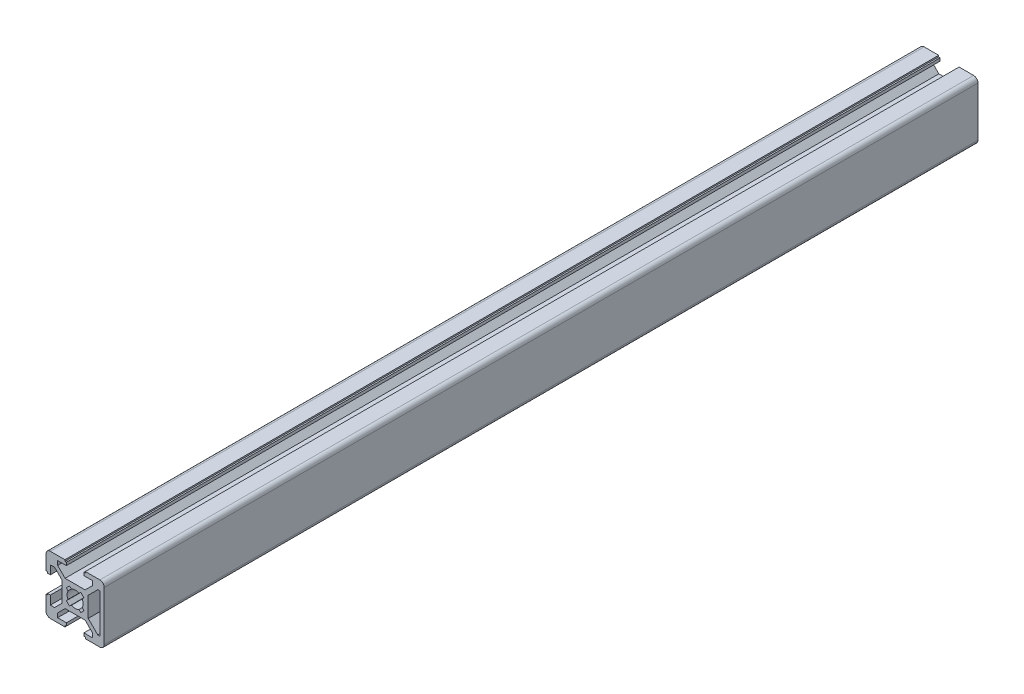
SolidWorks part; units mm, degrees
ref_plane "Front Plane" through (0, 0, 0) normal (0, 0, 1) x (1, 0, 0)
ref_plane "Top Plane" through (0, 0, 0) normal (0, 1, 0) x (1, 0, 0)
ref_plane "Right Plane" through (0, 0, 0) normal (1, 0, 0) x (0, 0, -1)
sketch "Sketch1" plane through (0, 0, 0) normal (0, 0, 1) x (1, 0, 0)
  line L12 (8.5, 6.7322) -> (7.7929, 6.7322)
  line L13 (8.5, -6.7322) -> (8.5, 6.7322)
  line L14 (7.7929, -6.7322) -> (8.5, -6.7322)
  line L15 (4.5, -3.4393) -> (7.7929, -6.7322)
  line L16 (4.5, 3.4393) -> (4.5, -3.4393)
  line L17 (7.7929, 6.7322) -> (4.5, 3.4393)
  line L36 (-3.0002, 1.9496) -> (-2.4356, 1.2768)
  line L37 (-1.9496, 3.0002) -> (-3.0002, 1.9496)
  line L38 (-1.2768, 2.4356) -> (-1.9496, 3.0002)
  line L39 (1.9496, 3.0002) -> (1.2768, 2.4356)
  line L40 (3.0002, 1.9496) -> (1.9496, 3.0002)
  line L41 (2.4356, 1.2768) -> (3.0002, 1.9496)
  line L42 (3.0002, -1.9496) -> (2.4356, -1.2768)
  line L43 (1.9496, -3.0002) -> (3.0002, -1.9496)
  line L44 (1.2768, -2.4356) -> (1.9496, -3.0002)
  line L45 (-1.9496, -3.0002) -> (-1.2768, -2.4356)
  line L46 (-3.0002, -1.9496) -> (-1.9496, -3.0002)
  line L47 (-2.4356, -1.2768) -> (-3.0002, -1.9496)
  line L128 (-3.4393, -4.5) -> (3.4393, -4.5)
  line L129 (3.4393, -4.5) -> (6, -7.0607)
  line L130 (6, -7.0607) -> (6, -8.5)
  line L131 (6, -8.5) -> (3, -8.5)
  line L132 (3, -8.5) -> (3, -9.5)
  line L133 (3, -9.5) -> (3.5, -9.5)
  line L134 (3.5, -9.5) -> (3.5, -10)
  line L135 (3.5, -10) -> (8.5, -10)
  line L136 (10, -8.5) -> (10, 8.5)
  line L137 (8.5, 10) -> (3.5, 10)
  line L138 (3.5, 10) -> (3.5, 9.5)
  line L139 (3.5, 9.5) -> (3, 9.5)
  line L140 (3, 9.5) -> (3, 8.5)
  line L141 (3, 8.5) -> (6, 8.5)
  line L142 (6, 8.5) -> (6, 7.0607)
  line L143 (6, 7.0607) -> (3.4393, 4.5)
  line L144 (3.4393, 4.5) -> (-3.4393, 4.5)
  line L145 (-3.4393, 4.5) -> (-6, 7.0607)
  line L146 (-6, 7.0607) -> (-6, 8.5)
  line L147 (-6, 8.5) -> (-3, 8.5)
  line L148 (-3, 8.5) -> (-3, 9.5)
  line L149 (-3, 9.5) -> (-3.5, 9.5)
  line L150 (-3.5, 9.5) -> (-3.5, 10)
  line L151 (-3.5, 10) -> (-8.5, 10)
  line L152 (-10, 8.5) -> (-10, 3.5)
  line L153 (-10, 3.5) -> (-9.5, 3.5)
  line L154 (-9.5, 3.5) -> (-9.5, 3)
  line L155 (-9.5, 3) -> (-8.5, 3)
  line L156 (-8.5, 3) -> (-8.5, 6)
  line L157 (-8.5, 6) -> (-7.0607, 6)
  line L158 (-7.0607, 6) -> (-4.5, 3.4393)
  line L159 (-4.5, 3.4393) -> (-4.5, -3.4393)
  line L160 (-4.5, -3.4393) -> (-7.0607, -6)
  line L161 (-7.0607, -6) -> (-8.5, -6)
  line L162 (-8.5, -6) -> (-8.5, -3)
  line L163 (-8.5, -3) -> (-9.5, -3)
  line L164 (-9.5, -3) -> (-9.5, -3.5)
  line L165 (-9.5, -3.5) -> (-10, -3.5)
  line L166 (-10, -3.5) -> (-10, -8.5)
  line L167 (-8.5, -10) -> (-3.5, -10)
  line L168 (-3.5, -10) -> (-3.5, -9.5)
  line L169 (-3.5, -9.5) -> (-3, -9.5)
  line L170 (-3, -9.5) -> (-3, -8.5)
  line L171 (-3, -8.5) -> (-6, -8.5)
  line L172 (-6, -8.5) -> (-6, -7.0607)
  line L173 (-6, -7.0607) -> (-3.4393, -4.5)
  arc A8 (-2.4356, 1.2768) -> (-2.4356, -1.2768) centre (0, 0) ccw
  arc A9 (1.2768, 2.4356) -> (-1.2768, 2.4356) centre (0, 0) ccw
  arc A10 (2.4356, -1.2768) -> (2.4356, 1.2768) centre (0, 0) ccw
  arc A11 (-1.2768, -2.4356) -> (1.2768, -2.4356) centre (0, 0) ccw
  arc A16 (8.5, -10) -> (10, -8.5) centre (8.5, -8.5) ccw
  arc A17 (10, 8.5) -> (8.5, 10) centre (8.5, 8.5) ccw
  arc A18 (-8.5, 10) -> (-10, 8.5) centre (-8.5, 8.5) ccw
  arc A19 (-10, -8.5) -> (-8.5, -10) centre (-8.5, -8.5) ccw
extrude "Boss-Extrude1" add sketch "Sketch1" along normal blind 3000
sketch "Sketch2" plane through (0, 0, 3000) normal (0, 0, 1) x (1, 0, 0)
  line L46 (-6, -7.0607) -> (-3.4393, -4.5)
  line L47 (-3.4393, -4.5) -> (3.4393, -4.5)
  line L48 (3.4393, -4.5) -> (6, -7.0607)
  line L49 (6, -7.0607) -> (6, -8.5)
  line L50 (6, -8.5) -> (3, -8.5)
  line L51 (3, -8.5) -> (3, -9.5)
  line L52 (3, -9.5) -> (3.5, -9.5)
  line L53 (3.5, -9.5) -> (3.5, -10)
  line L54 (3.5, -10) -> (8.5, -10)
  line L55 (10, -8.5) -> (10, 8.5)
  line L56 (8.5, 10) -> (3.5, 10)
  line L57 (3.5, 10) -> (3.5, 9.5)
  line L58 (3.5, 9.5) -> (3, 9.5)
  line L59 (3, 9.5) -> (3, 8.5)
  line L60 (3, 8.5) -> (6, 8.5)
  line L61 (6, 8.5) -> (6, 7.0607)
  line L62 (6, 7.0607) -> (3.4393, 4.5)
  line L63 (3.4393, 4.5) -> (-3.4393, 4.5)
  line L64 (-3.4393, 4.5) -> (-6, 7.0607)
  line L65 (-6, 7.0607) -> (-6, 8.5)
  line L66 (-6, 8.5) -> (-3, 8.5)
  line L67 (-3, 8.5) -> (-3, 9.5)
  line L68 (-3, 9.5) -> (-3.5, 9.5)
  line L69 (-3.5, 9.5) -> (-3.5, 10)
  line L70 (-3.5, 10) -> (-8.5, 10)
  line L71 (-10, 8.5) -> (-10, 3.5)
  line L72 (-10, 3.5) -> (-9.5, 3.5)
  line L73 (-9.5, 3.5) -> (-9.5, 3)
  line L74 (-9.5, 3) -> (-8.5, 3)
  line L75 (-8.5, 3) -> (-8.5, 6)
  line L76 (-8.5, 6) -> (-7.0607, 6)
  line L77 (-7.0607, 6) -> (-4.5, 3.4393)
  line L78 (-4.5, 3.4393) -> (-4.5, -3.4393)
  line L79 (-4.5, -3.4393) -> (-7.0607, -6)
  line L80 (-7.0607, -6) -> (-8.5, -6)
  line L81 (-8.5, -6) -> (-8.5, -3)
  line L82 (-8.5, -3) -> (-9.5, -3)
  line L83 (-9.5, -3) -> (-9.5, -3.5)
  line L84 (-9.5, -3.5) -> (-10, -3.5)
  line L85 (-10, -3.5) -> (-10, -8.5)
  line L86 (-8.5, -10) -> (-3.5, -10)
  line L87 (-3.5, -10) -> (-3.5, -9.5)
  line L88 (-3.5, -9.5) -> (-3, -9.5)
  line L89 (-3, -9.5) -> (-3, -8.5)
  line L90 (-3, -8.5) -> (-6, -8.5)
  line L91 (-6, -8.5) -> (-6, -7.0607)
  line L92 (-6, -7.0607) -> (-3.4393, -4.5)
  line L93 (-3.4393, -4.5) -> (3.4393, -4.5)
  line L94 (3.4393, -4.5) -> (6, -7.0607)
  line L95 (6, -7.0607) -> (6, -8.5)
  line L96 (6, -8.5) -> (3, -8.5)
  line L97 (3, -8.5) -> (3, -9.5)
  line L98 (3, -9.5) -> (3.5, -9.5)
  line L99 (3.5, -9.5) -> (3.5, -10)
  line L100 (3.5, -10) -> (8.5, -10)
  line L101 (10, -8.5) -> (10, 8.5)
  line L102 (8.5, 10) -> (3.5, 10)
  line L103 (3.5, 10) -> (3.5, 9.5)
  line L104 (3.5, 9.5) -> (3, 9.5)
  line L105 (3, 9.5) -> (3, 8.5)
  line L106 (3, 8.5) -> (6, 8.5)
  line L107 (6, 8.5) -> (6, 7.0607)
  line L108 (6, 7.0607) -> (3.4393, 4.5)
  line L109 (3.4393, 4.5) -> (-3.4393, 4.5)
  line L110 (-3.4393, 4.5) -> (-6, 7.0607)
  line L111 (-6, 7.0607) -> (-6, 8.5)
  line L112 (-6, 8.5) -> (-3, 8.5)
  line L113 (-3, 8.5) -> (-3, 9.5)
  line L114 (-3, 9.5) -> (-3.5, 9.5)
  line L115 (-3.5, 9.5) -> (-3.5, 10)
  line L116 (-3.5, 10) -> (-8.5, 10)
  line L117 (-10, 8.5) -> (-10, 3.5)
  line L118 (-10, 3.5) -> (-9.5, 3.5)
  line L119 (-9.5, 3.5) -> (-9.5, 3)
  line L120 (-9.5, 3) -> (-8.5, 3)
  line L121 (-8.5, 3) -> (-8.5, 6)
  line L122 (-8.5, 6) -> (-7.0607, 6)
  line L123 (-7.0607, 6) -> (-4.5, 3.4393)
  line L124 (-4.5, 3.4393) -> (-4.5, -3.4393)
  line L125 (-4.5, -3.4393) -> (-7.0607, -6)
  line L126 (-7.0607, -6) -> (-8.5, -6)
  line L127 (-8.5, -6) -> (-8.5, -3)
  line L128 (-8.5, -3) -> (-9.5, -3)
  line L129 (-9.5, -3) -> (-9.5, -3.5)
  line L130 (-9.5, -3.5) -> (-10, -3.5)
  line L131 (-10, -3.5) -> (-10, -8.5)
  line L132 (-8.5, -10) -> (-3.5, -10)
  line L133 (-3.5, -10) -> (-3.5, -9.5)
  line L134 (-3.5, -9.5) -> (-3, -9.5)
  line L135 (-3, -9.5) -> (-3, -8.5)
  line L136 (-3, -8.5) -> (-6, -8.5)
  line L137 (-6, -8.5) -> (-6, -7.0607)
  arc A4 (8.5, -10) -> (10, -8.5) centre (8.5, -8.5) ccw
  arc A5 (10, 8.5) -> (8.5, 10) centre (8.5, 8.5) ccw
  arc A6 (-8.5, 10) -> (-10, 8.5) centre (-8.5, 8.5) ccw
  arc A7 (-10, -8.5) -> (-8.5, -10) centre (-8.5, -8.5) ccw
  arc A8 (8.5, -10) -> (10, -8.5) centre (8.5, -8.5) ccw
  arc A9 (10, 8.5) -> (8.5, 10) centre (8.5, 8.5) ccw
  arc A10 (-8.5, 10) -> (-10, 8.5) centre (-8.5, 8.5) ccw
  arc A11 (-10, -8.5) -> (-8.5, -10) centre (-8.5, -8.5) ccw
  dimension "D1" = 0
extrude "Cut-Extrude1" cut sketch "Sketch2" against normal offset from surface (2700 mm away) 300 up to face at (6.931, 0, 0)
sketch "Sketch3" [suppressed] plane through (0, 0, 3000) normal (0, 0, 1) x (1, 0, 0)
  line L46 (-6, -7.0607) -> (-3.4393, -4.5)
  line L47 (-3.4393, -4.5) -> (3.4393, -4.5)
  line L48 (3.4393, -4.5) -> (6, -7.0607)
  line L49 (6, -7.0607) -> (6, -8.5)
  line L50 (6, -8.5) -> (3, -8.5)
  line L51 (3, -8.5) -> (3, -9.5)
  line L52 (3, -9.5) -> (3.5, -9.5)
  line L53 (3.5, -9.5) -> (3.5, -10)
  line L54 (3.5, -10) -> (8.5, -10)
  line L55 (10, -8.5) -> (10, 8.5)
  line L56 (8.5, 10) -> (3.5, 10)
  line L57 (3.5, 10) -> (3.5, 9.5)
  line L58 (3.5, 9.5) -> (3, 9.5)
  line L59 (3, 9.5) -> (3, 8.5)
  line L60 (3, 8.5) -> (6, 8.5)
  line L61 (6, 8.5) -> (6, 7.0607)
  line L62 (6, 7.0607) -> (3.4393, 4.5)
  line L63 (3.4393, 4.5) -> (-3.4393, 4.5)
  line L64 (-3.4393, 4.5) -> (-6, 7.0607)
  line L65 (-6, 7.0607) -> (-6, 8.5)
  line L66 (-6, 8.5) -> (-3, 8.5)
  line L67 (-3, 8.5) -> (-3, 9.5)
  line L68 (-3, 9.5) -> (-3.5, 9.5)
  line L69 (-3.5, 9.5) -> (-3.5, 10)
  line L70 (-3.5, 10) -> (-8.5, 10)
  line L71 (-10, 8.5) -> (-10, 3.5)
  line L72 (-10, 3.5) -> (-9.5, 3.5)
  line L73 (-9.5, 3.5) -> (-9.5, 3)
  line L74 (-9.5, 3) -> (-8.5, 3)
  line L75 (-8.5, 3) -> (-8.5, 6)
  line L76 (-8.5, 6) -> (-7.0607, 6)
  line L77 (-7.0607, 6) -> (-4.5, 3.4393)
  line L78 (-4.5, 3.4393) -> (-4.5, -3.4393)
  line L79 (-4.5, -3.4393) -> (-7.0607, -6)
  line L80 (-7.0607, -6) -> (-8.5, -6)
  line L81 (-8.5, -6) -> (-8.5, -3)
  line L82 (-8.5, -3) -> (-9.5, -3)
  line L83 (-9.5, -3) -> (-9.5, -3.5)
  line L84 (-9.5, -3.5) -> (-10, -3.5)
  line L85 (-10, -3.5) -> (-10, -8.5)
  line L86 (-8.5, -10) -> (-3.5, -10)
  line L87 (-3.5, -10) -> (-3.5, -9.5)
  line L88 (-3.5, -9.5) -> (-3, -9.5)
  line L89 (-3, -9.5) -> (-3, -8.5)
  line L90 (-3, -8.5) -> (-6, -8.5)
  line L91 (-6, -8.5) -> (-6, -7.0607)
  line L92 (-6, -7.0607) -> (-3.4393, -4.5)
  line L93 (-3.4393, -4.5) -> (3.4393, -4.5)
  line L94 (3.4393, -4.5) -> (6, -7.0607)
  line L95 (6, -7.0607) -> (6, -8.5)
  line L96 (6, -8.5) -> (3, -8.5)
  line L97 (3, -8.5) -> (3, -9.5)
  line L98 (3, -9.5) -> (3.5, -9.5)
  line L99 (3.5, -9.5) -> (3.5, -10)
  line L100 (3.5, -10) -> (8.5, -10)
  line L101 (10, -8.5) -> (10, 8.5)
  line L102 (8.5, 10) -> (3.5, 10)
  line L103 (3.5, 10) -> (3.5, 9.5)
  line L104 (3.5, 9.5) -> (3, 9.5)
  line L105 (3, 9.5) -> (3, 8.5)
  line L106 (3, 8.5) -> (6, 8.5)
  line L107 (6, 8.5) -> (6, 7.0607)
  line L108 (6, 7.0607) -> (3.4393, 4.5)
  line L109 (3.4393, 4.5) -> (-3.4393, 4.5)
  line L110 (-3.4393, 4.5) -> (-6, 7.0607)
  line L111 (-6, 7.0607) -> (-6, 8.5)
  line L112 (-6, 8.5) -> (-3, 8.5)
  line L113 (-3, 8.5) -> (-3, 9.5)
  line L114 (-3, 9.5) -> (-3.5, 9.5)
  line L115 (-3.5, 9.5) -> (-3.5, 10)
  line L116 (-3.5, 10) -> (-8.5, 10)
  line L117 (-10, 8.5) -> (-10, 3.5)
  line L118 (-10, 3.5) -> (-9.5, 3.5)
  line L119 (-9.5, 3.5) -> (-9.5, 3)
  line L120 (-9.5, 3) -> (-8.5, 3)
  line L121 (-8.5, 3) -> (-8.5, 6)
  line L122 (-8.5, 6) -> (-7.0607, 6)
  line L123 (-7.0607, 6) -> (-4.5, 3.4393)
  line L124 (-4.5, 3.4393) -> (-4.5, -3.4393)
  line L125 (-4.5, -3.4393) -> (-7.0607, -6)
  line L126 (-7.0607, -6) -> (-8.5, -6)
  line L127 (-8.5, -6) -> (-8.5, -3)
  line L128 (-8.5, -3) -> (-9.5, -3)
  line L129 (-9.5, -3) -> (-9.5, -3.5)
  line L130 (-9.5, -3.5) -> (-10, -3.5)
  line L131 (-10, -3.5) -> (-10, -8.5)
  line L132 (-8.5, -10) -> (-3.5, -10)
  line L133 (-3.5, -10) -> (-3.5, -9.5)
  line L134 (-3.5, -9.5) -> (-3, -9.5)
  line L135 (-3, -9.5) -> (-3, -8.5)
  line L136 (-3, -8.5) -> (-6, -8.5)
  line L137 (-6, -8.5) -> (-6, -7.0607)
  arc A4 (8.5, -10) -> (10, -8.5) centre (8.5, -8.5) ccw
  arc A5 (10, 8.5) -> (8.5, 10) centre (8.5, 8.5) ccw
  arc A6 (-8.5, 10) -> (-10, 8.5) centre (-8.5, 8.5) ccw
  arc A7 (-10, -8.5) -> (-8.5, -10) centre (-8.5, -8.5) ccw
  arc A8 (8.5, -10) -> (10, -8.5) centre (8.5, -8.5) ccw
  arc A9 (10, 8.5) -> (8.5, 10) centre (8.5, 8.5) ccw
  arc A10 (-8.5, 10) -> (-10, 8.5) centre (-8.5, 8.5) ccw
  arc A11 (-10, -8.5) -> (-8.5, -10) centre (-8.5, -8.5) ccw
  dimension "D1" = 0
extrude "Cut-Extrude2" [suppressed] cut sketch "Sketch3" against normal offset from surface (2500 mm away) 500
sketch "Sketch5" [suppressed] plane through (0, 0, 3000) normal (0, 0, 1) x (1, 0, 0)
  line L46 (-6, -7.0607) -> (-3.4393, -4.5)
  line L47 (-3.4393, -4.5) -> (3.4393, -4.5)
  line L48 (3.4393, -4.5) -> (6, -7.0607)
  line L49 (6, -7.0607) -> (6, -8.5)
  line L50 (6, -8.5) -> (3, -8.5)
  line L51 (3, -8.5) -> (3, -9.5)
  line L52 (3, -9.5) -> (3.5, -9.5)
  line L53 (3.5, -9.5) -> (3.5, -10)
  line L54 (3.5, -10) -> (8.5, -10)
  line L55 (10, -8.5) -> (10, 8.5)
  line L56 (8.5, 10) -> (3.5, 10)
  line L57 (3.5, 10) -> (3.5, 9.5)
  line L58 (3.5, 9.5) -> (3, 9.5)
  line L59 (3, 9.5) -> (3, 8.5)
  line L60 (3, 8.5) -> (6, 8.5)
  line L61 (6, 8.5) -> (6, 7.0607)
  line L62 (6, 7.0607) -> (3.4393, 4.5)
  line L63 (3.4393, 4.5) -> (-3.4393, 4.5)
  line L64 (-3.4393, 4.5) -> (-6, 7.0607)
  line L65 (-6, 7.0607) -> (-6, 8.5)
  line L66 (-6, 8.5) -> (-3, 8.5)
  line L67 (-3, 8.5) -> (-3, 9.5)
  line L68 (-3, 9.5) -> (-3.5, 9.5)
  line L69 (-3.5, 9.5) -> (-3.5, 10)
  line L70 (-3.5, 10) -> (-8.5, 10)
  line L71 (-10, 8.5) -> (-10, 3.5)
  line L72 (-10, 3.5) -> (-9.5, 3.5)
  line L73 (-9.5, 3.5) -> (-9.5, 3)
  line L74 (-9.5, 3) -> (-8.5, 3)
  line L75 (-8.5, 3) -> (-8.5, 6)
  line L76 (-8.5, 6) -> (-7.0607, 6)
  line L77 (-7.0607, 6) -> (-4.5, 3.4393)
  line L78 (-4.5, 3.4393) -> (-4.5, -3.4393)
  line L79 (-4.5, -3.4393) -> (-7.0607, -6)
  line L80 (-7.0607, -6) -> (-8.5, -6)
  line L81 (-8.5, -6) -> (-8.5, -3)
  line L82 (-8.5, -3) -> (-9.5, -3)
  line L83 (-9.5, -3) -> (-9.5, -3.5)
  line L84 (-9.5, -3.5) -> (-10, -3.5)
  line L85 (-10, -3.5) -> (-10, -8.5)
  line L86 (-8.5, -10) -> (-3.5, -10)
  line L87 (-3.5, -10) -> (-3.5, -9.5)
  line L88 (-3.5, -9.5) -> (-3, -9.5)
  line L89 (-3, -9.5) -> (-3, -8.5)
  line L90 (-3, -8.5) -> (-6, -8.5)
  line L91 (-6, -8.5) -> (-6, -7.0607)
  line L92 (-6, -7.0607) -> (-3.4393, -4.5)
  line L93 (-3.4393, -4.5) -> (3.4393, -4.5)
  line L94 (3.4393, -4.5) -> (6, -7.0607)
  line L95 (6, -7.0607) -> (6, -8.5)
  line L96 (6, -8.5) -> (3, -8.5)
  line L97 (3, -8.5) -> (3, -9.5)
  line L98 (3, -9.5) -> (3.5, -9.5)
  line L99 (3.5, -9.5) -> (3.5, -10)
  line L100 (3.5, -10) -> (8.5, -10)
  line L101 (10, -8.5) -> (10, 8.5)
  line L102 (8.5, 10) -> (3.5, 10)
  line L103 (3.5, 10) -> (3.5, 9.5)
  line L104 (3.5, 9.5) -> (3, 9.5)
  line L105 (3, 9.5) -> (3, 8.5)
  line L106 (3, 8.5) -> (6, 8.5)
  line L107 (6, 8.5) -> (6, 7.0607)
  line L108 (6, 7.0607) -> (3.4393, 4.5)
  line L109 (3.4393, 4.5) -> (-3.4393, 4.5)
  line L110 (-3.4393, 4.5) -> (-6, 7.0607)
  line L111 (-6, 7.0607) -> (-6, 8.5)
  line L112 (-6, 8.5) -> (-3, 8.5)
  line L113 (-3, 8.5) -> (-3, 9.5)
  line L114 (-3, 9.5) -> (-3.5, 9.5)
  line L115 (-3.5, 9.5) -> (-3.5, 10)
  line L116 (-3.5, 10) -> (-8.5, 10)
  line L117 (-10, 8.5) -> (-10, 3.5)
  line L118 (-10, 3.5) -> (-9.5, 3.5)
  line L119 (-9.5, 3.5) -> (-9.5, 3)
  line L120 (-9.5, 3) -> (-8.5, 3)
  line L121 (-8.5, 3) -> (-8.5, 6)
  line L122 (-8.5, 6) -> (-7.0607, 6)
  line L123 (-7.0607, 6) -> (-4.5, 3.4393)
  line L124 (-4.5, 3.4393) -> (-4.5, -3.4393)
  line L125 (-4.5, -3.4393) -> (-7.0607, -6)
  line L126 (-7.0607, -6) -> (-8.5, -6)
  line L127 (-8.5, -6) -> (-8.5, -3)
  line L128 (-8.5, -3) -> (-9.5, -3)
  line L129 (-9.5, -3) -> (-9.5, -3.5)
  line L130 (-9.5, -3.5) -> (-10, -3.5)
  line L131 (-10, -3.5) -> (-10, -8.5)
  line L132 (-8.5, -10) -> (-3.5, -10)
  line L133 (-3.5, -10) -> (-3.5, -9.5)
  line L134 (-3.5, -9.5) -> (-3, -9.5)
  line L135 (-3, -9.5) -> (-3, -8.5)
  line L136 (-3, -8.5) -> (-6, -8.5)
  line L137 (-6, -8.5) -> (-6, -7.0607)
  arc A4 (8.5, -10) -> (10, -8.5) centre (8.5, -8.5) ccw
  arc A5 (10, 8.5) -> (8.5, 10) centre (8.5, 8.5) ccw
  arc A6 (-8.5, 10) -> (-10, 8.5) centre (-8.5, 8.5) ccw
  arc A7 (-10, -8.5) -> (-8.5, -10) centre (-8.5, -8.5) ccw
  arc A8 (8.5, -10) -> (10, -8.5) centre (8.5, -8.5) ccw
  arc A9 (10, 8.5) -> (8.5, 10) centre (8.5, 8.5) ccw
  arc A10 (-8.5, 10) -> (-10, 8.5) centre (-8.5, 8.5) ccw
  arc A11 (-10, -8.5) -> (-8.5, -10) centre (-8.5, -8.5) ccw
  dimension "D1" = 0
extrude "Cut-Extrude4" [suppressed] cut sketch "Sketch5" against normal offset from surface (2918 mm away) 82
sketch "Sketch6" [suppressed] plane through (0, 0, 3000) normal (0, 0, 1) x (1, 0, 0)
  line L46 (-6, -7.0607) -> (-3.4393, -4.5)
  line L47 (-3.4393, -4.5) -> (3.4393, -4.5)
  line L48 (3.4393, -4.5) -> (6, -7.0607)
  line L49 (6, -7.0607) -> (6, -8.5)
  line L50 (6, -8.5) -> (3, -8.5)
  line L51 (3, -8.5) -> (3, -9.5)
  line L52 (3, -9.5) -> (3.5, -9.5)
  line L53 (3.5, -9.5) -> (3.5, -10)
  line L54 (3.5, -10) -> (8.5, -10)
  line L55 (10, -8.5) -> (10, 8.5)
  line L56 (8.5, 10) -> (3.5, 10)
  line L57 (3.5, 10) -> (3.5, 9.5)
  line L58 (3.5, 9.5) -> (3, 9.5)
  line L59 (3, 9.5) -> (3, 8.5)
  line L60 (3, 8.5) -> (6, 8.5)
  line L61 (6, 8.5) -> (6, 7.0607)
  line L62 (6, 7.0607) -> (3.4393, 4.5)
  line L63 (3.4393, 4.5) -> (-3.4393, 4.5)
  line L64 (-3.4393, 4.5) -> (-6, 7.0607)
  line L65 (-6, 7.0607) -> (-6, 8.5)
  line L66 (-6, 8.5) -> (-3, 8.5)
  line L67 (-3, 8.5) -> (-3, 9.5)
  line L68 (-3, 9.5) -> (-3.5, 9.5)
  line L69 (-3.5, 9.5) -> (-3.5, 10)
  line L70 (-3.5, 10) -> (-8.5, 10)
  line L71 (-10, 8.5) -> (-10, 3.5)
  line L72 (-10, 3.5) -> (-9.5, 3.5)
  line L73 (-9.5, 3.5) -> (-9.5, 3)
  line L74 (-9.5, 3) -> (-8.5, 3)
  line L75 (-8.5, 3) -> (-8.5, 6)
  line L76 (-8.5, 6) -> (-7.0607, 6)
  line L77 (-7.0607, 6) -> (-4.5, 3.4393)
  line L78 (-4.5, 3.4393) -> (-4.5, -3.4393)
  line L79 (-4.5, -3.4393) -> (-7.0607, -6)
  line L80 (-7.0607, -6) -> (-8.5, -6)
  line L81 (-8.5, -6) -> (-8.5, -3)
  line L82 (-8.5, -3) -> (-9.5, -3)
  line L83 (-9.5, -3) -> (-9.5, -3.5)
  line L84 (-9.5, -3.5) -> (-10, -3.5)
  line L85 (-10, -3.5) -> (-10, -8.5)
  line L86 (-8.5, -10) -> (-3.5, -10)
  line L87 (-3.5, -10) -> (-3.5, -9.5)
  line L88 (-3.5, -9.5) -> (-3, -9.5)
  line L89 (-3, -9.5) -> (-3, -8.5)
  line L90 (-3, -8.5) -> (-6, -8.5)
  line L91 (-6, -8.5) -> (-6, -7.0607)
  line L92 (-6, -7.0607) -> (-3.4393, -4.5)
  line L93 (-3.4393, -4.5) -> (3.4393, -4.5)
  line L94 (3.4393, -4.5) -> (6, -7.0607)
  line L95 (6, -7.0607) -> (6, -8.5)
  line L96 (6, -8.5) -> (3, -8.5)
  line L97 (3, -8.5) -> (3, -9.5)
  line L98 (3, -9.5) -> (3.5, -9.5)
  line L99 (3.5, -9.5) -> (3.5, -10)
  line L100 (3.5, -10) -> (8.5, -10)
  line L101 (10, -8.5) -> (10, 8.5)
  line L102 (8.5, 10) -> (3.5, 10)
  line L103 (3.5, 10) -> (3.5, 9.5)
  line L104 (3.5, 9.5) -> (3, 9.5)
  line L105 (3, 9.5) -> (3, 8.5)
  line L106 (3, 8.5) -> (6, 8.5)
  line L107 (6, 8.5) -> (6, 7.0607)
  line L108 (6, 7.0607) -> (3.4393, 4.5)
  line L109 (3.4393, 4.5) -> (-3.4393, 4.5)
  line L110 (-3.4393, 4.5) -> (-6, 7.0607)
  line L111 (-6, 7.0607) -> (-6, 8.5)
  line L112 (-6, 8.5) -> (-3, 8.5)
  line L113 (-3, 8.5) -> (-3, 9.5)
  line L114 (-3, 9.5) -> (-3.5, 9.5)
  line L115 (-3.5, 9.5) -> (-3.5, 10)
  line L116 (-3.5, 10) -> (-8.5, 10)
  line L117 (-10, 8.5) -> (-10, 3.5)
  line L118 (-10, 3.5) -> (-9.5, 3.5)
  line L119 (-9.5, 3.5) -> (-9.5, 3)
  line L120 (-9.5, 3) -> (-8.5, 3)
  line L121 (-8.5, 3) -> (-8.5, 6)
  line L122 (-8.5, 6) -> (-7.0607, 6)
  line L123 (-7.0607, 6) -> (-4.5, 3.4393)
  line L124 (-4.5, 3.4393) -> (-4.5, -3.4393)
  line L125 (-4.5, -3.4393) -> (-7.0607, -6)
  line L126 (-7.0607, -6) -> (-8.5, -6)
  line L127 (-8.5, -6) -> (-8.5, -3)
  line L128 (-8.5, -3) -> (-9.5, -3)
  line L129 (-9.5, -3) -> (-9.5, -3.5)
  line L130 (-9.5, -3.5) -> (-10, -3.5)
  line L131 (-10, -3.5) -> (-10, -8.5)
  line L132 (-8.5, -10) -> (-3.5, -10)
  line L133 (-3.5, -10) -> (-3.5, -9.5)
  line L134 (-3.5, -9.5) -> (-3, -9.5)
  line L135 (-3, -9.5) -> (-3, -8.5)
  line L136 (-3, -8.5) -> (-6, -8.5)
  line L137 (-6, -8.5) -> (-6, -7.0607)
  arc A4 (8.5, -10) -> (10, -8.5) centre (8.5, -8.5) ccw
  arc A5 (10, 8.5) -> (8.5, 10) centre (8.5, 8.5) ccw
  arc A6 (-8.5, 10) -> (-10, 8.5) centre (-8.5, 8.5) ccw
  arc A7 (-10, -8.5) -> (-8.5, -10) centre (-8.5, -8.5) ccw
  arc A8 (8.5, -10) -> (10, -8.5) centre (8.5, -8.5) ccw
  arc A9 (10, 8.5) -> (8.5, 10) centre (8.5, 8.5) ccw
  arc A10 (-8.5, 10) -> (-10, 8.5) centre (-8.5, 8.5) ccw
  arc A11 (-10, -8.5) -> (-8.5, -10) centre (-8.5, -8.5) ccw
  dimension "D1" = 0
extrude "Cut-Extrude5" [suppressed] cut sketch "Sketch6" against normal offset from surface (2775 mm away) 225
sketch "Sketch7" [suppressed] plane through (0, 0, 3000) normal (0, 0, 1) x (1, 0, 0)
  line L46 (-6, -7.0607) -> (-3.4393, -4.5)
  line L47 (-3.4393, -4.5) -> (3.4393, -4.5)
  line L48 (3.4393, -4.5) -> (6, -7.0607)
  line L49 (6, -7.0607) -> (6, -8.5)
  line L50 (6, -8.5) -> (3, -8.5)
  line L51 (3, -8.5) -> (3, -9.5)
  line L52 (3, -9.5) -> (3.5, -9.5)
  line L53 (3.5, -9.5) -> (3.5, -10)
  line L54 (3.5, -10) -> (8.5, -10)
  line L55 (10, -8.5) -> (10, 8.5)
  line L56 (8.5, 10) -> (3.5, 10)
  line L57 (3.5, 10) -> (3.5, 9.5)
  line L58 (3.5, 9.5) -> (3, 9.5)
  line L59 (3, 9.5) -> (3, 8.5)
  line L60 (3, 8.5) -> (6, 8.5)
  line L61 (6, 8.5) -> (6, 7.0607)
  line L62 (6, 7.0607) -> (3.4393, 4.5)
  line L63 (3.4393, 4.5) -> (-3.4393, 4.5)
  line L64 (-3.4393, 4.5) -> (-6, 7.0607)
  line L65 (-6, 7.0607) -> (-6, 8.5)
  line L66 (-6, 8.5) -> (-3, 8.5)
  line L67 (-3, 8.5) -> (-3, 9.5)
  line L68 (-3, 9.5) -> (-3.5, 9.5)
  line L69 (-3.5, 9.5) -> (-3.5, 10)
  line L70 (-3.5, 10) -> (-8.5, 10)
  line L71 (-10, 8.5) -> (-10, 3.5)
  line L72 (-10, 3.5) -> (-9.5, 3.5)
  line L73 (-9.5, 3.5) -> (-9.5, 3)
  line L74 (-9.5, 3) -> (-8.5, 3)
  line L75 (-8.5, 3) -> (-8.5, 6)
  line L76 (-8.5, 6) -> (-7.0607, 6)
  line L77 (-7.0607, 6) -> (-4.5, 3.4393)
  line L78 (-4.5, 3.4393) -> (-4.5, -3.4393)
  line L79 (-4.5, -3.4393) -> (-7.0607, -6)
  line L80 (-7.0607, -6) -> (-8.5, -6)
  line L81 (-8.5, -6) -> (-8.5, -3)
  line L82 (-8.5, -3) -> (-9.5, -3)
  line L83 (-9.5, -3) -> (-9.5, -3.5)
  line L84 (-9.5, -3.5) -> (-10, -3.5)
  line L85 (-10, -3.5) -> (-10, -8.5)
  line L86 (-8.5, -10) -> (-3.5, -10)
  line L87 (-3.5, -10) -> (-3.5, -9.5)
  line L88 (-3.5, -9.5) -> (-3, -9.5)
  line L89 (-3, -9.5) -> (-3, -8.5)
  line L90 (-3, -8.5) -> (-6, -8.5)
  line L91 (-6, -8.5) -> (-6, -7.0607)
  line L92 (-6, -7.0607) -> (-3.4393, -4.5)
  line L93 (-3.4393, -4.5) -> (3.4393, -4.5)
  line L94 (3.4393, -4.5) -> (6, -7.0607)
  line L95 (6, -7.0607) -> (6, -8.5)
  line L96 (6, -8.5) -> (3, -8.5)
  line L97 (3, -8.5) -> (3, -9.5)
  line L98 (3, -9.5) -> (3.5, -9.5)
  line L99 (3.5, -9.5) -> (3.5, -10)
  line L100 (3.5, -10) -> (8.5, -10)
  line L101 (10, -8.5) -> (10, 8.5)
  line L102 (8.5, 10) -> (3.5, 10)
  line L103 (3.5, 10) -> (3.5, 9.5)
  line L104 (3.5, 9.5) -> (3, 9.5)
  line L105 (3, 9.5) -> (3, 8.5)
  line L106 (3, 8.5) -> (6, 8.5)
  line L107 (6, 8.5) -> (6, 7.0607)
  line L108 (6, 7.0607) -> (3.4393, 4.5)
  line L109 (3.4393, 4.5) -> (-3.4393, 4.5)
  line L110 (-3.4393, 4.5) -> (-6, 7.0607)
  line L111 (-6, 7.0607) -> (-6, 8.5)
  line L112 (-6, 8.5) -> (-3, 8.5)
  line L113 (-3, 8.5) -> (-3, 9.5)
  line L114 (-3, 9.5) -> (-3.5, 9.5)
  line L115 (-3.5, 9.5) -> (-3.5, 10)
  line L116 (-3.5, 10) -> (-8.5, 10)
  line L117 (-10, 8.5) -> (-10, 3.5)
  line L118 (-10, 3.5) -> (-9.5, 3.5)
  line L119 (-9.5, 3.5) -> (-9.5, 3)
  line L120 (-9.5, 3) -> (-8.5, 3)
  line L121 (-8.5, 3) -> (-8.5, 6)
  line L122 (-8.5, 6) -> (-7.0607, 6)
  line L123 (-7.0607, 6) -> (-4.5, 3.4393)
  line L124 (-4.5, 3.4393) -> (-4.5, -3.4393)
  line L125 (-4.5, -3.4393) -> (-7.0607, -6)
  line L126 (-7.0607, -6) -> (-8.5, -6)
  line L127 (-8.5, -6) -> (-8.5, -3)
  line L128 (-8.5, -3) -> (-9.5, -3)
  line L129 (-9.5, -3) -> (-9.5, -3.5)
  line L130 (-9.5, -3.5) -> (-10, -3.5)
  line L131 (-10, -3.5) -> (-10, -8.5)
  line L132 (-8.5, -10) -> (-3.5, -10)
  line L133 (-3.5, -10) -> (-3.5, -9.5)
  line L134 (-3.5, -9.5) -> (-3, -9.5)
  line L135 (-3, -9.5) -> (-3, -8.5)
  line L136 (-3, -8.5) -> (-6, -8.5)
  line L137 (-6, -8.5) -> (-6, -7.0607)
  arc A4 (8.5, -10) -> (10, -8.5) centre (8.5, -8.5) ccw
  arc A5 (10, 8.5) -> (8.5, 10) centre (8.5, 8.5) ccw
  arc A6 (-8.5, 10) -> (-10, 8.5) centre (-8.5, 8.5) ccw
  arc A7 (-10, -8.5) -> (-8.5, -10) centre (-8.5, -8.5) ccw
  arc A8 (8.5, -10) -> (10, -8.5) centre (8.5, -8.5) ccw
  arc A9 (10, 8.5) -> (8.5, 10) centre (8.5, 8.5) ccw
  arc A10 (-8.5, 10) -> (-10, 8.5) centre (-8.5, 8.5) ccw
  arc A11 (-10, -8.5) -> (-8.5, -10) centre (-8.5, -8.5) ccw
  dimension "D1" = 0
extrude "Cut-Extrude6" [suppressed] cut sketch "Sketch7" against normal offset from surface (2810 mm away) 190
